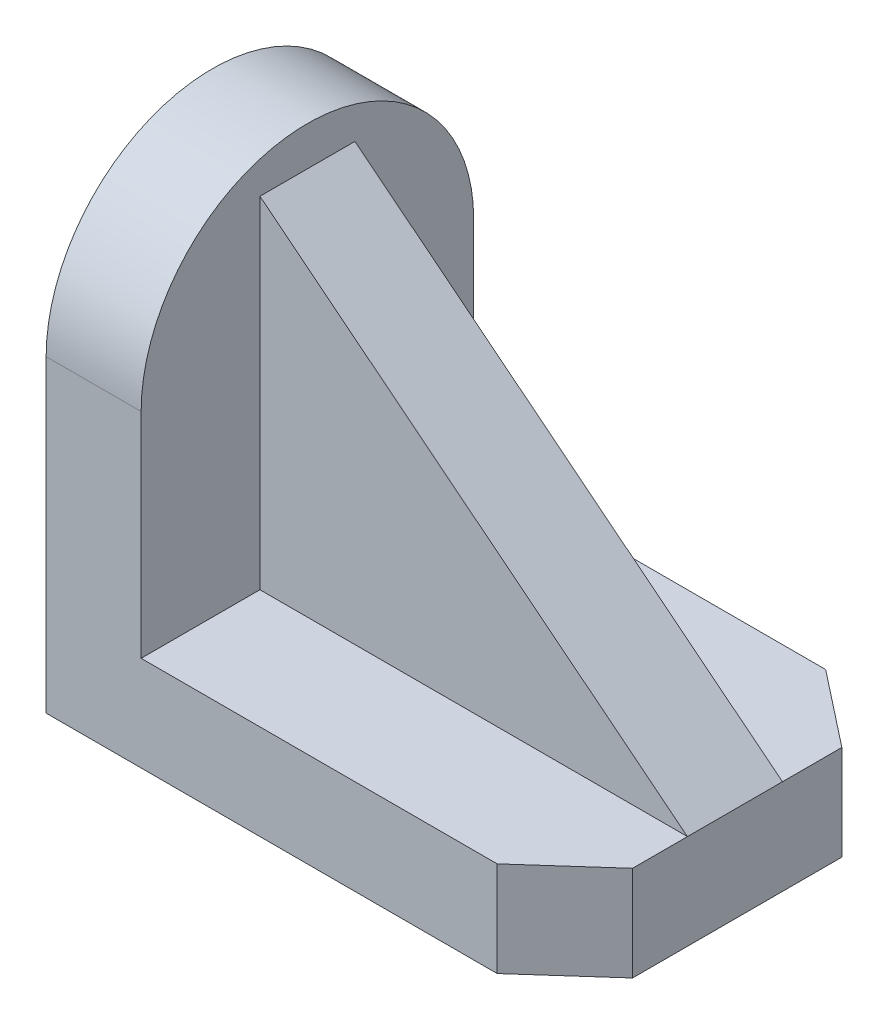
SolidWorks part; units mm, degrees
ref_plane "Front Plane" through (0, 0, 0) normal (0, 0, 1) x (1, 0, 0)
ref_plane "Top Plane" through (0, 0, 0) normal (0, 1, 0) x (1, 0, 0)
ref_plane "Right Plane" through (0, 0, 0) normal (1, 0, 0) x (0, 0, -1)
sketch "Sketch1" plane through (0, 0, 0) normal (0, 1, 0) x (1, 0, 0)
  line L1 (-33, 21) -> (33, 21)
  line L2 (-33, 21) -> (-33, -21)
  line L3 (-33, -21) -> (33, -21)
  line L4 (33, 21) -> (33, -21)
  line L5 (-33, 21) -> (33, -21) construction
  line L6 (-33, -21) -> (33, 21) construction
  point P0 (0, 0)
  dimension "D1" = 66
  dimension "D2" = 42
extrude "Boss-Extrude1" add sketch "Sketch1" along normal blind 12 contours L2 L3 L4 L1
sketch "Sketch2" plane through (0, 12, 0) normal (0, 1, 0) x (1, 0, 0)
  line L0 (-33, 21) -> (-33, -21) construction
  line L1 (-33, -21) -> (33, -21) construction
  line L2 (-33, 21) -> (-21, 21)
  line L3 (-33, 21) -> (-33, -21)
  line L4 (-33, -21) -> (-21, -21)
  line L5 (-21, 21) -> (-21, -21)
  dimension "D1" = 12
extrude "Boss-Extrude2" add sketch "Sketch2" along normal blind 26.995
sketch "Sketch4" plane through (-21, 0, 0) normal (1, 0, 0) x (0, 0, -1)
  line L0 (-21, 38.995) -> (21, 38.995) construction
  circle A0 centre (0, 38.995) radius 21
extrude "Boss-Extrude8" add sketch "Sketch4" against normal blind 12 contours A0
sketch "Sketch8" plane through (0, 0, 0) normal (0, 0, 1) x (1, 0, 0)
  line L0 (-21, 12) -> (-21, 55.039)
  line L1 (-21, 38.995) -> (-21, 59.995) construction
  line L2 (-21, 55.039) -> (33, 12)
  line L3 (33, 12) -> (-21, 12)
extrude "Boss-Extrude9" add sketch "Sketch8" along normal mid plane 12
sketch "Sketch12" plane through (0, 12, 0) normal (0, 1, 0) x (1, 0, 0)
  line L0 (33, -12.9358) -> (33, -21)
  line L1 (33, -21) -> (23.9654, -21)
  line L2 (33, 13.5) -> (33, 21)
  line L3 (33, 21) -> (23.4551, 21)
  line L4 (-21, 21) -> (33, 21) construction
  line L5 (23.9654, -21) -> (33, -12.9358)
  line L6 (33, 13.5) -> (23.4551, 21)
extrude "Cut-Extrude1" cut sketch "Sketch12" against normal blind 12
